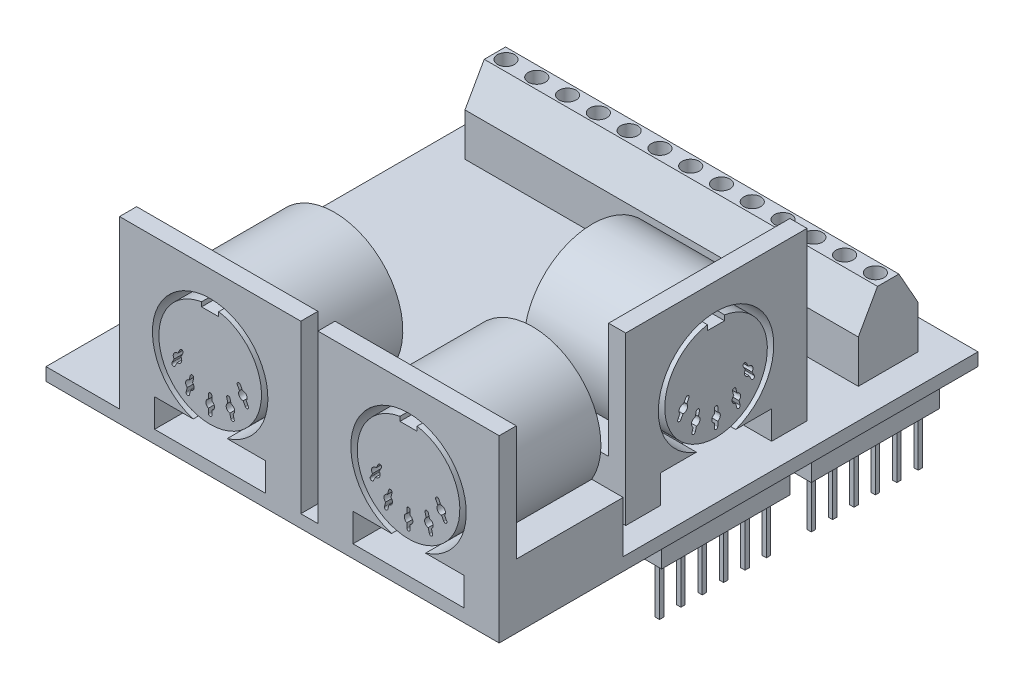
SolidWorks part; units mm, degrees
ref_plane "Front Plane" through (0, 0, 0) normal (0, 0, 1) x (1, 0, 0)
ref_plane "Top Plane" through (0, 0, 0) normal (0, 1, 0) x (1, 0, 0)
ref_plane "Right Plane" through (0, 0, 0) normal (1, 0, 0) x (0, 0, -1)
sketch "Sketch1" plane through (0, 0, 0) normal (0, 1, 0) x (1, 0, 0)
  line L1 (-26.5, -28) -> (26.5, -28)
  line L2 (-26.5, -28) -> (-26.5, 28)
  line L3 (-26.5, 28) -> (26.5, 28)
  line L4 (26.5, -28) -> (26.5, 28)
  line L5 (-26.5, -28) -> (26.5, 28) construction
  line L6 (-26.5, 28) -> (26.5, -28) construction
  point P0 (0, 0)
  dimension "D1" = 53
  dimension "D2" = 56
extrude "Boss-Extrude1" add sketch "Sketch1" along normal blind 1.5
sketch "Sketch2" plane through (0, 1.5, 0) normal (0, 1, 0) x (1, 0, 0)
  line L0 (-26.5, 28) -> (-26.5, -28) construction
  line L1 (-23, 24.5) -> (23, 24.5)
  line L2 (-23, 24.5) -> (-23, 17.5)
  line L3 (-23, 17.5) -> (23, 17.5)
  line L4 (23, 24.5) -> (23, 17.5)
  line L5 (26.5, -28) -> (26.5, 28) construction
  line L6 (26.5, 28) -> (-26.5, 28) construction
  dimension "D1" = 3.5
  dimension "D2" = 3.5
  dimension "D3" = 3.5
  dimension "D4" = 7
extrude "Boss-Extrude2" add sketch "Sketch2" along normal blind 5
sketch "Sketch4" plane through (-23, 0, 0) normal (-1, 0, 0) x (0, 0, 1)
  line L0 (-24.5, 6.5) -> (-17.5, 6.5)
  line L1 (-17.5, 6.5) -> (-19.75, 10.5)
  line L2 (-19.75, 10.5) -> (-22.25, 10.5)
  line L3 (-22.25, 10.5) -> (-24.5, 6.5)
  line L4 (-21, 10.5) -> (-21, 6.5) construction
  dimension "D1" = 4
  dimension "D2" = 2.5
extrude "Boss-Extrude3" add sketch "Sketch4" against normal up to surface (46 mm away) up to face at (23, 4, -21)
sketch "Sketch5" plane through (0, 10.5, 0) normal (0, 1, 0) x (1, 0, 0)
  line L0 (-23, 21) -> (23, 21) construction
  line L1 (-23, 24.5) -> (-23, 17.5) construction
  line L2 (23, 22.25) -> (23, 19.75) construction
  circle A0 centre (-21.7, 21) radius 1
  circle A1 centre (-18.1, 21) radius 1
  circle A2 centre (-14.5, 21) radius 1
  circle A3 centre (-10.9, 21) radius 1
  circle A4 centre (-7.3, 21) radius 1
  circle A5 centre (-3.7, 21) radius 1
  circle A6 centre (-0.1, 21) radius 1
  circle A7 centre (3.5, 21) radius 1
  circle A8 centre (7.1, 21) radius 1
  circle A9 centre (10.7, 21) radius 1
  circle A10 centre (14.3, 21) radius 1
  circle A11 centre (17.9, 21) radius 1
  circle A12 centre (21.5, 21) radius 1
  dimension "D1" = 2
  dimension "D2" = 1.3
  dimension "D3" = 13
extrude "Cut-Extrude1" cut sketch "Sketch5" against normal blind 2
sketch "Sketch6" plane through (0, 0, 28) normal (0, 0, 1) x (1, 0, 0)
  line L0 (-26.5, 1.5) -> (26.5, 1.5) construction
  line L1 (-17.9, 1.5) -> (3.3, 1.5)
  line L2 (-17.9, 1.5) -> (-17.9, 21)
  line L3 (-17.9, 21) -> (3.3, 21)
  line L4 (3.3, 1.5) -> (3.3, 21)
  line L5 (-23, 1.5) -> (23, 1.5) construction
  line L6 (5.3, 1.5) -> (26.5, 1.5)
  line L7 (5.3, 1.5) -> (5.3, 21)
  line L8 (5.3, 21) -> (26.5, 21)
  line L9 (26.5, 1.5) -> (26.5, 21)
  dimension "D1" = 21.2
  dimension "D2" = 19.5
  dimension "D3" = 21.2
  dimension "D4" = 19.5
  dimension "D5" = 2
extrude "Boss-Extrude4" add sketch "Sketch6" against normal blind 2 separate body
sketch "Sketch7" plane through (0, 0, 26) normal (0, 0, -1) x (-1, 0, 0)
  line L0 (-15.9, 21) -> (-15.9, 1.5) construction
  line L1 (-26.5, 21) -> (-5.3, 21) construction
  line L2 (-23, 1.5) -> (23, 1.5) construction
  line L3 (-15.9, 11.5) -> (7.2714, 11.5) construction
  line L4 (7.3, 21) -> (7.3, 7.5) construction
  line L5 (-3.3, 21) -> (17.9, 21) construction
  line L7 (-5.3, 21) -> (-5.3, 1.5) construction
  line L8 (-26.5, 1.5) -> (-5.3, 1.5)
  line L9 (-26.5, 1.5) -> (-26.5, 7.5)
  line L10 (-26.5, 7.5) -> (-22.8282, 7.5)
  line L12 (-5.3, 1.5) -> (-5.3, 7.5)
  line L13 (-8.9718, 7.5) -> (-5.3, 7.5)
  line L14 (-26.5, 1.5) -> (26.5, 1.5) construction
  line L15 (17.9, 7.5) -> (14.1996, 7.5)
  line L16 (17.9, 7.5) -> (17.9, 1.5)
  line L17 (17.9, 1.5) -> (-3.3, 1.5)
  line L18 (-3.3, 7.5) -> (-3.3, 1.5)
  line L19 (-3.3, 1.5) -> (-3.3, 21) construction
  line L20 (17.9, 21) -> (17.9, 1.5) construction
  line L21 (0.3432, 7.5) -> (-3.3, 7.5)
  line L22 (7.3, 3.5001) -> (7.3, 1.5) construction
  arc A0 (-8.9718, 7.5) -> (-22.8282, 7.5) centre (-15.9, 11.5) ccw
  arc A1 (14.1996, 7.5) -> (0.3432, 7.5) centre (7.2714, 11.5) ccw
  point P6 (-15.9, 11.5)
  dimension "D2" = 16
  dimension "D3" = 16
  dimension "D1" = 10
  dimension "D4" = 6
extrude "Boss-Extrude5" add sketch "Sketch7" along normal blind 12.5
sketch "Sketch8" plane through (0, 0, 28) normal (0, 0, 1) x (1, 0, 0)
  line L0 (-17.9, 21) -> (3.3, 1.5) construction
  line L1 (3.3, 21) -> (-17.9, 1.5) construction
  line L2 (-7.3, 17.25) -> (-7.3, 16.65) construction
  line L3 (-8.3, 16.65) -> (-6.3, 16.65)
  line L4 (-6.3, 16.65) -> (-6.3, 17.1661)
  line L5 (-8.3, 16.65) -> (-8.3, 17.1661)
  line L6 (-11.1219, 10.0698) -> (-3.4781, 10.0698) construction
  line L7 (-9.6748, 8.0313) -> (-4.9252, 8.0313) construction
  line L8 (-11.1219, 10.0698) -> (-9.6748, 8.0313) construction
  line L9 (-9.6748, 8.0313) -> (-7.3, 7.25) construction
  line L10 (-7.3, 7.25) -> (-4.9252, 8.0313) construction
  line L11 (-4.9252, 8.0313) -> (-3.4781, 10.0698) construction
  line L12 (-7.3, 6.25) -> (-7.3, 8.25) construction
  line L13 (-7.5, 6.25) -> (-7.5, 6.7917)
  line L14 (-7.1, 6.25) -> (-7.1, 6.7917)
  line L15 (-4.6757, 7.0629) -> (-5.1747, 8.9996) construction
  line L16 (-4.8694, 7.013) -> (-5.0046, 7.5376)
  line L17 (-4.4821, 7.1128) -> (-4.6172, 7.6374)
  line L18 (-3.0082, 9.1871) -> (-3.9479, 10.9526) construction
  line L19 (-3.1847, 9.0931) -> (-3.4393, 9.5713)
  line L20 (-2.8316, 9.2811) -> (-3.0862, 9.7593)
  line L21 (-9.9243, 7.0629) -> (-9.4253, 8.9996) construction
  line L22 (-10.1179, 7.1128) -> (-9.9828, 7.6374)
  line L23 (-9.7306, 7.013) -> (-9.5954, 7.5376)
  line L24 (-11.5918, 9.1871) -> (-10.6521, 10.9526) construction
  line L25 (-11.7684, 9.2811) -> (-11.5138, 9.7593)
  line L26 (-11.4153, 9.0931) -> (-11.1607, 9.5713)
  line L27 (-7.3, 17.25) -> (-10.6521, 10.9526) construction
  line L28 (-7.3, 17.25) -> (-3.9479, 10.9526) construction
  line L29 (-7.3, 17.25) -> (-9.4253, 8.9996) construction
  line L30 (-7.3, 17.25) -> (-5.1747, 8.9996) construction
  line L31 (-11.0832, 10.5683) -> (-10.8286, 11.0465)
  line L32 (-10.7301, 10.3804) -> (-10.4755, 10.8586)
  line L33 (4.3, 1.5) -> (4.3, 27.7192) construction
  line L34 (-9.7542, 8.5249) -> (-9.619, 9.0495)
  line L35 (-9.3668, 8.4251) -> (-9.2317, 8.9497)
  line L36 (3.3, 1.5) -> (5.3, 1.5) construction
  line L37 (15.9, 1.5) -> (15.9, 11.25) construction
  line L38 (-7.5, 7.7083) -> (-7.5, 8.25)
  line L39 (-7.1, 7.7083) -> (-7.1, 8.25)
  line L40 (15.9, 17.25) -> (13.7747, 8.9996) construction
  line L41 (15.9, 17.25) -> (18.0253, 8.9996) construction
  line L42 (-5.2332, 8.4251) -> (-5.3683, 8.9497)
  line L43 (-4.8458, 8.5249) -> (-4.981, 9.0495)
  line L44 (15.9, 17.25) -> (12.5479, 10.9526) construction
  line L45 (15.9, 17.25) -> (19.2521, 10.9526) construction
  line L46 (-3.8699, 10.3804) -> (-4.1245, 10.8586)
  line L47 (-3.5168, 10.5683) -> (-3.7714, 11.0465)
  line L48 (20.1918, 9.1871) -> (19.2521, 10.9526) construction
  line L49 (18.5243, 7.0629) -> (18.0253, 8.9996) construction
  line L50 (11.6082, 9.1871) -> (12.5479, 10.9526) construction
  line L51 (13.2757, 7.0629) -> (13.7747, 8.9996) construction
  line L52 (15.9, 6.25) -> (15.9, 8.25) construction
  line L53 (13.5252, 8.0313) -> (12.0781, 10.0698) construction
  line L54 (15.9, 7.25) -> (13.5252, 8.0313) construction
  line L55 (18.2748, 8.0313) -> (15.9, 7.25) construction
  line L56 (19.7219, 10.0698) -> (18.2748, 8.0313) construction
  line L57 (18.2748, 8.0313) -> (13.5252, 8.0313) construction
  line L58 (19.7219, 10.0698) -> (12.0781, 10.0698) construction
  line L59 (15.9, 17.25) -> (15.9, 16.65) construction
  line L60 (17.89, 4.8) -> (22.4, 4.8)
  line L61 (22.4, 4.8) -> (22.4, 1.5)
  line L62 (9.4, 4.8) -> (13.91, 4.8)
  line L63 (9.4, 1.5) -> (9.4, 4.8)
  line L64 (22.4, 1.5) -> (9.4, 1.5)
  line L65 (12.1168, 10.5683) -> (12.3714, 11.0465)
  line L66 (12.4699, 10.3804) -> (12.7245, 10.8586)
  line L67 (13.4458, 8.5249) -> (13.581, 9.0495)
  line L68 (13.8332, 8.4251) -> (13.9683, 8.9497)
  line L69 (15.7, 7.7083) -> (15.7, 8.25)
  line L70 (16.1, 7.7083) -> (16.1, 8.25)
  line L71 (17.9668, 8.4251) -> (17.8317, 8.9497)
  line L72 (18.3542, 8.5249) -> (18.219, 9.0495)
  line L73 (19.3301, 10.3804) -> (19.0755, 10.8586)
  line L74 (19.6832, 10.5683) -> (19.4286, 11.0465)
  line L75 (20.0153, 9.0931) -> (19.7607, 9.5713)
  line L76 (20.3684, 9.2811) -> (20.1138, 9.7593)
  line L77 (18.3306, 7.013) -> (18.1954, 7.5376)
  line L78 (18.7179, 7.1128) -> (18.5828, 7.6374)
  line L79 (11.4316, 9.2811) -> (11.6862, 9.7593)
  line L80 (11.7847, 9.0931) -> (12.0393, 9.5713)
  line L81 (13.0821, 7.1128) -> (13.2172, 7.6374)
  line L82 (-17.9, 1.5) -> (3.3, 1.5) construction
  line L83 (-13.8, 1.5) -> (-0.8, 1.5)
  line L84 (-0.8, 1.5) -> (-0.8, 4.8)
  line L85 (-0.8, 4.8) -> (-5.31, 4.8)
  line L86 (-13.8, 4.8) -> (-13.8, 1.5)
  line L87 (-7.3, 1.5) -> (-7.3, 11.25) construction
  line L88 (-9.29, 4.8) -> (-13.8, 4.8)
  line L89 (13.4694, 7.013) -> (13.6046, 7.5376)
  line L90 (15.7, 6.25) -> (15.7, 6.7917)
  line L91 (16.1, 6.25) -> (16.1, 6.7917)
  line L92 (16.9, 16.65) -> (16.9, 17.1661)
  line L93 (14.9, 16.65) -> (14.9, 17.1661)
  line L94 (16.9, 16.65) -> (14.9, 16.65)
  arc A0 (-5.31, 4.8) -> (-9.29, 4.8) centre (-7.3, 11.25) ccw
  arc A1 (-8.3, 17.1661) -> (-6.3, 17.1661) centre (-7.3, 11.25) ccw
  arc A2 (-7.5, 7.7083) -> (-7.5, 6.7917) centre (-7.3, 7.25) ccw
  arc A3 (-9.5954, 7.5376) -> (-9.3668, 8.4251) centre (-9.6748, 8.0313) ccw
  arc A4 (-4.8005, 7.5471) -> (-4.8458, 8.5249) centre (-4.9252, 8.0313) ccw
  arc A5 (-3.0862, 9.7593) -> (-3.5168, 10.5683) centre (-3.4781, 10.0698) ccw
  arc A6 (-11.0832, 10.5683) -> (-11.5138, 9.7593) centre (-11.1219, 10.0698) ccw
  circle A7 centre (-7.3, 11.25) radius 4 construction
  arc A8 (-7.5, 6.25) -> (-7.1, 6.25) centre (-7.3, 6.25) ccw
  arc A9 (-7.1, 8.25) -> (-7.5, 8.25) centre (-7.3, 8.25) ccw
  arc A10 (-4.8694, 7.013) -> (-4.4821, 7.1128) centre (-4.6757, 7.0629) ccw
  arc A11 (-4.981, 9.0495) -> (-5.3683, 8.9497) centre (-5.1747, 8.9996) ccw
  arc A12 (-3.1847, 9.0931) -> (-2.8316, 9.2811) centre (-3.0082, 9.1871) ccw
  arc A13 (-3.7714, 11.0465) -> (-4.1245, 10.8586) centre (-3.9479, 10.9526) ccw
  arc A14 (-10.1179, 7.1128) -> (-9.7306, 7.013) centre (-9.9243, 7.0629) ccw
  arc A15 (-9.2317, 8.9497) -> (-9.619, 9.0495) centre (-9.4253, 8.9996) ccw
  arc A16 (-11.7684, 9.2811) -> (-11.4153, 9.0931) centre (-11.5918, 9.1871) ccw
  arc A17 (-10.4755, 10.8586) -> (-10.8286, 11.0465) centre (-10.6521, 10.9526) ccw
  arc A18 (-11.1607, 9.5713) -> (-10.7301, 10.3804) centre (-11.1219, 10.0698) ccw
  arc A19 (-9.7542, 8.5249) -> (-9.9828, 7.6374) centre (-9.6748, 8.0313) ccw
  arc A20 (-7.1, 6.7917) -> (-7.1, 7.7083) centre (-7.3, 7.25) ccw
  arc A21 (-5.2332, 8.4251) -> (-5.0046, 7.5376) centre (-4.9252, 8.0313) ccw
  arc A22 (-3.8699, 10.3804) -> (-3.4393, 9.5713) centre (-3.4781, 10.0698) ccw
  circle A23 centre (15.9, 11.25) radius 4 construction
  arc A24 (12.4699, 10.3804) -> (12.0393, 9.5713) centre (12.0781, 10.0698) cw
  arc A25 (13.8332, 8.4251) -> (13.6046, 7.5376) centre (13.5252, 8.0313) cw
  arc A26 (15.7, 6.7917) -> (15.7, 7.7083) centre (15.9, 7.25) cw
  arc A27 (18.3542, 8.5249) -> (18.5828, 7.6374) centre (18.2748, 8.0313) cw
  arc A28 (19.7607, 9.5713) -> (19.3301, 10.3804) centre (19.7219, 10.0698) cw
  arc A29 (19.0755, 10.8586) -> (19.4286, 11.0465) centre (19.2521, 10.9526) cw
  arc A30 (20.3684, 9.2811) -> (20.0153, 9.0931) centre (20.1918, 9.1871) cw
  arc A31 (17.8317, 8.9497) -> (18.219, 9.0495) centre (18.0253, 8.9996) cw
  arc A32 (18.7179, 7.1128) -> (18.3306, 7.013) centre (18.5243, 7.0629) cw
  arc A33 (12.3714, 11.0465) -> (12.7245, 10.8586) centre (12.5479, 10.9526) cw
  arc A34 (11.7847, 9.0931) -> (11.4316, 9.2811) centre (11.6082, 9.1871) cw
  arc A35 (13.581, 9.0495) -> (13.9683, 8.9497) centre (13.7747, 8.9996) cw
  arc A36 (13.4694, 7.013) -> (13.0821, 7.1128) centre (13.2757, 7.0629) cw
  arc A37 (15.7, 8.25) -> (16.1, 8.25) centre (15.9, 8.25) cw
  arc A38 (16.1, 6.25) -> (15.7, 6.25) centre (15.9, 6.25) cw
  arc A39 (19.6832, 10.5683) -> (20.1138, 9.7593) centre (19.7219, 10.0698) cw
  arc A40 (11.6862, 9.7593) -> (12.1168, 10.5683) centre (12.0781, 10.0698) cw
  arc A41 (13.4005, 7.5471) -> (13.4458, 8.5249) centre (13.5252, 8.0313) cw
  arc A42 (18.1954, 7.5376) -> (17.9668, 8.4251) centre (18.2748, 8.0313) cw
  arc A43 (16.1, 7.7083) -> (16.1, 6.7917) centre (15.9, 7.25) cw
  arc A44 (16.9, 17.1661) -> (14.9, 17.1661) centre (15.9, 11.25) cw
  arc A45 (13.91, 4.8) -> (17.89, 4.8) centre (15.9, 11.25) cw
  point P8 (-7.3, 11.25)
  point P30 (-7.3, 7.25)
  point P37 (-4.9252, 8.0313)
  point P44 (-3.4781, 10.0698)
  point P50 (-9.6748, 8.0313)
  point P58 (-11.1219, 10.0698)
  dimension "D1" = 13.5
  dimension "D2" = 12
  dimension "D4" = 1
  dimension "D5" = 8
  dimension "D8" = 0.2
  dimension "D3" = 2
  dimension "D6" = 2.5
  dimension "D7" = 2
  dimension "D9" = 3.3
  dimension "D10" = 13
  dimension "D11" = 0.6
extrude "Cut-Extrude2" cut sketch "Sketch8" against normal blind 5
sketch "Sketch9" plane through (26.5, 0, 0) normal (1, 0, 0) x (0, 0, -1)
  line L0 (-13.5, 1.5) -> (28, 1.5) construction
  line L1 (-10.2, 1.5) -> (11, 1.5)
  line L2 (-10.2, 1.5) -> (-10.2, 21)
  line L3 (-10.2, 21) -> (11, 21)
  line L4 (11, 1.5) -> (11, 21)
  line L5 (-26, 21) -> (-28, 21) construction
  line L7 (-28, 21) -> (-28, 0) construction
  dimension "D1" = 21.2
  dimension "D2" = 39
extrude "Boss-Extrude6" add sketch "Sketch9" against normal blind 2 from offset 3 separate body offset against normal yes
sketch "Sketch11" plane through (21.5, 0, 0) normal (-1, 0, 0) x (0, 0, 1)
  line L0 (-0.4, 21) -> (-0.4, 1.5) construction
  line L1 (-11, 21) -> (10.2, 21) construction
  line L2 (10.2, 1.5) -> (-11, 1.5) construction
  line L3 (10.2, 21) -> (10.2, 1.5) construction
  line L4 (-11, 1.5) -> (10.2, 1.5)
  line L5 (-11, 1.5) -> (-11, 7.5)
  line L6 (-11, 7.5) -> (-7.3282, 7.5)
  line L7 (10.2, 1.5) -> (10.2, 7.5)
  line L8 (6.5282, 7.5) -> (10.2, 7.5)
  arc A0 (6.5282, 7.5) -> (-7.3282, 7.5) centre (-0.4, 11.5) ccw
  dimension "D2" = 16
  dimension "D1" = 10
  dimension "D3" = 6
extrude "Boss-Extrude7" add sketch "Sketch11" along normal blind 12.5
sketch "Sketch13" plane through (23.5, 0, 0) normal (1, 0, 0) x (0, 0, -1)
  line L0 (-10.2, 21) -> (11, 1.5) construction
  line L1 (-10.2, 1.5) -> (11, 1.5) construction
  line L2 (0.3632, 16.1486) -> (0.3632, 1.5) construction
  line L3 (-6.1, 1.5) -> (6.8265, 1.5)
  line L7 (0.3632, 17.0631) -> (0.3632, 16.4631) construction
  line L8 (-0.6368, 16.4631) -> (1.3632, 16.4631)
  line L9 (1.3632, 16.4631) -> (1.3632, 17.0631)
  line L10 (-0.6368, 16.4631) -> (-0.6368, 17.0631)
  line L11 (-3.4587, 9.9668) -> (4.1852, 9.9668) construction
  line L12 (-2.0116, 7.9283) -> (2.738, 7.9283) construction
  line L13 (-3.4587, 9.9668) -> (-2.0116, 7.9283) construction
  line L14 (-2.0116, 7.9283) -> (0.3632, 7.147) construction
  line L15 (0.3632, 7.147) -> (2.738, 7.9283) construction
  line L16 (2.738, 7.9283) -> (4.1852, 9.9668) construction
  line L17 (0.3632, 6.147) -> (0.3632, 8.147) construction
  line L18 (0.1633, 6.1525) -> (0.1633, 6.6887)
  line L19 (0.5631, 6.1534) -> (0.5631, 6.6887)
  line L20 (2.9896, 6.9604) -> (2.4864, 8.8961) construction
  line L21 (2.7897, 6.9582) -> (2.6661, 7.4335)
  line L22 (3.186, 6.9982) -> (3.0465, 7.5348)
  line L23 (4.6594, 9.0864) -> (3.711, 10.8473) construction
  line L24 (4.4753, 9.0081) -> (4.2273, 9.4686)
  line L25 (4.8354, 9.1812) -> (4.5786, 9.6582)
  line L26 (-2.2632, 6.9604) -> (-1.7599, 8.8961) construction
  line L27 (-2.4567, 7.0108) -> (-2.3204, 7.535)
  line L28 (-2.0696, 6.9101) -> (-1.9333, 7.4344)
  line L29 (-3.9329, 9.0864) -> (-2.9845, 10.8473) construction
  line L30 (-4.1058, 9.1869) -> (-3.852, 9.6581)
  line L31 (-3.7568, 8.9916) -> (-3.4999, 9.4685)
  line L32 (0.3632, 17.0631) -> (-2.9845, 10.8473) construction
  line L33 (0.3632, 17.0631) -> (3.711, 10.8473) construction
  line L34 (0.3632, 17.0631) -> (-1.7599, 8.8961) construction
  line L35 (0.3632, 17.0631) -> (2.4864, 8.8961) construction
  line L36 (-3.4174, 10.4651) -> (-3.1636, 10.9363)
  line L37 (-3.0653, 10.2755) -> (-2.8084, 10.7524)
  line L38 (-2.0897, 8.4221) -> (-1.9519, 8.9523)
  line L39 (-1.7027, 8.3215) -> (-1.5664, 8.8458)
  line L40 (0.1633, 7.6053) -> (0.1633, 8.153)
  line L41 (0.5631, 7.6053) -> (0.5631, 8.1534)
  line L42 (2.4366, 8.3272) -> (2.2866, 8.9043)
  line L43 (2.8159, 8.4222) -> (2.6828, 8.9339)
  line L44 (3.7918, 10.2755) -> (3.5349, 10.7524)
  line L45 (4.144, 10.4651) -> (3.8871, 10.9421)
  line L46 (-6.1368, 1.5) -> (6.8632, 1.5)
  line L47 (6.8632, 1.5) -> (6.8632, 4.8)
  line L48 (6.8632, 4.8) -> (2.6606, 4.8)
  line L49 (-6.1368, 4.8) -> (-6.1368, 1.5)
  line L50 (0.3632, 1.5) -> (0.3632, 11.147) construction
  line L51 (-1.9342, 4.8) -> (-6.1368, 4.8)
  arc A2 (2.6606, 4.8) -> (-1.9342, 4.8) centre (0.3632, 11.147) ccw
  arc A3 (-0.6368, 17.0631) -> (1.3632, 17.0631) centre (0.3632, 11.147) ccw
  arc A4 (0.1633, 7.6053) -> (0.1633, 6.6887) centre (0.3632, 7.147) ccw
  arc A5 (-1.9333, 7.4344) -> (-1.7027, 8.3215) centre (-2.0116, 7.9283) ccw
  arc A6 (3.0465, 7.5348) -> (2.8159, 8.4222) centre (2.738, 7.9283) ccw
  arc A7 (4.5786, 9.6582) -> (4.144, 10.4651) centre (4.1852, 9.9668) ccw
  arc A8 (-3.4174, 10.4651) -> (-3.852, 9.6581) centre (-3.4587, 9.9668) ccw
  circle A9 centre (0.3632, 11.147) radius 4 construction
  arc A10 (0.1633, 6.1525) -> (0.5631, 6.1534) centre (0.3632, 6.147) ccw
  arc A11 (0.5631, 8.1534) -> (0.1633, 8.153) centre (0.3632, 8.147) ccw
  arc A12 (2.7897, 6.9582) -> (3.186, 6.9982) centre (2.9896, 6.9604) ccw
  arc A13 (2.6828, 8.9339) -> (2.2866, 8.9043) centre (2.4864, 8.8961) ccw
  arc A14 (4.4753, 9.0081) -> (4.8354, 9.1812) centre (4.6594, 9.0864) ccw
  arc A15 (3.8871, 10.9421) -> (3.5349, 10.7524) centre (3.711, 10.8473) ccw
  arc A16 (-2.4567, 7.0108) -> (-2.0696, 6.9101) centre (-2.2632, 6.9604) ccw
  arc A17 (-1.5664, 8.8458) -> (-1.9519, 8.9523) centre (-1.7599, 8.8961) ccw
  arc A18 (-4.1058, 9.1869) -> (-3.7568, 8.9916) centre (-3.9329, 9.0864) ccw
  arc A19 (-2.8084, 10.7524) -> (-3.1636, 10.9363) centre (-2.9845, 10.8473) ccw
  arc A20 (-3.4999, 9.4685) -> (-3.0653, 10.2755) centre (-3.4587, 9.9668) ccw
  arc A21 (-2.0897, 8.4221) -> (-2.3204, 7.535) centre (-2.0116, 7.9283) ccw
  arc A22 (0.5631, 6.6887) -> (0.5631, 7.6053) centre (0.3632, 7.147) ccw
  arc A23 (2.4366, 8.3272) -> (2.6661, 7.4335) centre (2.738, 7.9283) ccw
  arc A24 (3.7918, 10.2755) -> (4.2273, 9.4686) centre (4.1852, 9.9668) ccw
  point P15 (0.3632, 11.147)
  point P35 (0.3632, 7.147)
  point P42 (2.738, 7.9283)
  point P49 (4.1852, 9.9668)
  point P55 (-2.0116, 7.9283)
  point P63 (-3.4587, 9.9668)
  point P93 (0.4, 11.25)
  line M4 (-10.2, 1.5) -> (11, 1.5)
  dimension "D2" = 13
  dimension "D6" = 1
  dimension "D7" = 8
  dimension "D10" = 0.2
  dimension "D3" = 6.75
  dimension "D12" = 6
  dimension "D13" = 0.2
  dimension "D4" = 3.3
  dimension "D5" = 2
  dimension "D8" = 2.5
  dimension "D9" = 2
  dimension "D11" = 0.6
extrude "Cut-Extrude3" cut sketch "Sketch13" against normal blind 5 contours L48 A2 L51 L49 L47 A3 L10 L8 L9 M4 | L38 A21 L27 A16 L28 A5 L39 A17 | L31 A20 L37 A19 L36 A8 L30 A18 | L19 A22 L41 A11 L40 A4 L18 A10 | L42 A23 L21 A12 L22 A6 L43 A13 | L44 A24 L24 A14 L25 A7 L45 A15
sketch "Sketch14" plane through (0, 0, 0) normal (0, -1, 0) x (1, 0, 0)
  line L0 (25.5, 28) -> (25.5, -28) construction
  line L3 (-26.5, 28) -> (26.5, 28) construction
  line L4 (26.5, -28) -> (-26.5, -28) construction
  line L5 (-25.5, 28) -> (-25.5, -28) construction
  line L6 (26.5, 28) -> (26.5, -28) construction
  line L7 (-26.5, -28) -> (-26.5, 28) construction
  line L9 (-25.5, 18) -> (-23, 18)
  line L10 (-25.5, 18) -> (-25.5, -2)
  line L11 (-25.5, -2) -> (-23, -2)
  line L12 (-23, 18) -> (-23, -2)
  line L13 (25.5, 8) -> (23, 8)
  line L14 (25.5, 8) -> (25.5, -7)
  line L15 (25.5, -7) -> (23, -7)
  line L16 (23, 8) -> (23, -7)
  line L17 (25.5, -9.5) -> (23, -9.5)
  line L18 (25.5, -9.5) -> (25.5, -24.5)
  line L19 (25.5, -24.5) -> (23, -24.5)
  line L20 (23, -9.5) -> (23, -24.5)
  line L21 (-25.5, -4.5) -> (-23, -4.5)
  line L22 (-25.5, -4.5) -> (-25.5, -24.5)
  line L23 (-25.5, -24.5) -> (-23, -24.5)
  line L24 (-23, -4.5) -> (-23, -24.5)
  dimension "D1" = 1
  dimension "D2" = 1
  dimension "D3" = 2.5
  dimension "D4" = 20
  dimension "D5" = 15
  dimension "D6" = 3.5
  dimension "D7" = 15
  dimension "D8" = 2.5
  dimension "D9" = 10
  dimension "D10" = 2.5
  dimension "D11" = 20
  dimension "D12" = 2.5
  dimension "D13" = 20
  dimension "D14" = 3.5
extrude "Boss-Extrude8" add sketch "Sketch14" along normal blind 3
sketch "Sketch15" plane through (0, -3, 0) normal (0, -1, 0) x (1, 0, 0)
  line L0 (24.25, 8) -> (24.25, -24.5) construction
  line L1 (25.5, 8) -> (23, 8) construction
  line L2 (23, -24.5) -> (25.5, -24.5) construction
  line L3 (24, 4.75) -> (24.5, 4.75)
  line L4 (24, 7.25) -> (24.5, 7.25)
  line L5 (24, 7.25) -> (24, 6.75)
  line L6 (24, 6.75) -> (24.5, 6.75)
  line L7 (24.5, 7.25) -> (24.5, 6.75)
  line L8 (24, 7.25) -> (24.5, 6.75) construction
  line L9 (24, 6.75) -> (24.5, 7.25) construction
  line L10 (24, 4.75) -> (24, 4.25)
  line L11 (24, 4.25) -> (24.5, 4.25)
  line L12 (24.5, 4.75) -> (24.5, 4.25)
  line L13 (24, 4.75) -> (24.5, 4.25) construction
  line L14 (24, 4.25) -> (24.5, 4.75) construction
  line L15 (24, 2.25) -> (24.5, 2.25)
  line L16 (24, 2.25) -> (24, 1.75)
  line L17 (24, 1.75) -> (24.5, 1.75)
  line L18 (24.5, 2.25) -> (24.5, 1.75)
  line L19 (24, 2.25) -> (24.5, 1.75) construction
  line L20 (24, 1.75) -> (24.5, 2.25) construction
  line L21 (24, -0.25) -> (24.5, -0.25)
  line L22 (24, -0.25) -> (24, -0.75)
  line L23 (24, -0.75) -> (24.5, -0.75)
  line L24 (24.5, -0.25) -> (24.5, -0.75)
  line L25 (24, -0.25) -> (24.5, -0.75) construction
  line L26 (24, -0.75) -> (24.5, -0.25) construction
  line L27 (24, -2.75) -> (24.5, -2.75)
  line L28 (24, -2.75) -> (24, -3.25)
  line L29 (24, -3.25) -> (24.5, -3.25)
  line L30 (24.5, -2.75) -> (24.5, -3.25)
  line L31 (24, -2.75) -> (24.5, -3.25) construction
  line L32 (24, -3.25) -> (24.5, -2.75) construction
  line L33 (24, -5.25) -> (24.5, -5.25)
  line L34 (24, -5.25) -> (24, -5.75)
  line L35 (24, -5.75) -> (24.5, -5.75)
  line L36 (24.5, -5.25) -> (24.5, -5.75)
  line L37 (24, -5.25) -> (24.5, -5.75) construction
  line L38 (24, -5.75) -> (24.5, -5.25) construction
  line L42 (25.5, -9.5) -> (23, -9.5) construction
  line L43 (24, -10.5) -> (24.5, -10.5)
  line L44 (24, -10.5) -> (24, -11)
  line L45 (24, -11) -> (24.5, -11)
  line L46 (24.5, -10.5) -> (24.5, -11)
  line L47 (24, -10.5) -> (24.5, -11) construction
  line L48 (24, -11) -> (24.5, -10.5) construction
  line L49 (24, -13) -> (24, -13.5)
  line L50 (24, -13.5) -> (24.5, -13.5)
  line L51 (24.5, -13) -> (24.5, -13.5)
  line L52 (24, -13) -> (24.5, -13)
  line L53 (24, -15.5) -> (24, -16)
  line L54 (24, -16) -> (24.5, -16)
  line L55 (24.5, -15.5) -> (24.5, -16)
  line L56 (24, -15.5) -> (24.5, -15.5)
  line L57 (24, -18) -> (24, -18.5)
  line L58 (24, -18.5) -> (24.5, -18.5)
  line L59 (24.5, -18) -> (24.5, -18.5)
  line L60 (24, -18) -> (24.5, -18)
  line L61 (24, -20.5) -> (24, -21)
  line L62 (24, -21) -> (24.5, -21)
  line L63 (24.5, -20.5) -> (24.5, -21)
  line L64 (24, -20.5) -> (24.5, -20.5)
  line L65 (24, -23) -> (24, -23.5)
  line L66 (24, -23.5) -> (24.5, -23.5)
  line L67 (24.5, -23) -> (24.5, -23.5)
  line L68 (24, -23) -> (24.5, -23)
  line L70 (-24.25, 18) -> (-24.25, -24.5) construction
  line L71 (-23, 18) -> (-25.5, 18) construction
  line L72 (-25.5, -24.5) -> (-23, -24.5) construction
  line L73 (-24.5, 14.5) -> (-24, 14.5)
  line L74 (-24.5, 17) -> (-24, 17)
  line L75 (-24.5, 17) -> (-24.5, 16.5)
  line L76 (-24.5, 16.5) -> (-24, 16.5)
  line L77 (-24, 17) -> (-24, 16.5)
  line L78 (-24.5, 17) -> (-24, 16.5) construction
  line L79 (-24.5, 16.5) -> (-24, 17) construction
  line L80 (-24.5, 14.5) -> (-24.5, 14)
  line L81 (-24.5, 14) -> (-24, 14)
  line L82 (-24, 14.5) -> (-24, 14)
  line L83 (-24.5, 14.5) -> (-24, 14) construction
  line L84 (-24.5, 14) -> (-24, 14.5) construction
  line L85 (-24.5, 12) -> (-24, 12)
  line L86 (-24.5, 12) -> (-24.5, 11.5)
  line L87 (-24.5, 11.5) -> (-24, 11.5)
  line L88 (-24, 12) -> (-24, 11.5)
  line L89 (-24.5, 12) -> (-24, 11.5) construction
  line L90 (-24.5, 11.5) -> (-24, 12) construction
  line L91 (-24.5, 9.5) -> (-24, 9.5)
  line L92 (-24.5, 9.5) -> (-24.5, 9)
  line L93 (-24.5, 9) -> (-24, 9)
  line L94 (-24, 9.5) -> (-24, 9)
  line L95 (-24.5, 9.5) -> (-24, 9) construction
  line L96 (-24.5, 9) -> (-24, 9.5) construction
  line L97 (-24.5, 7) -> (-24, 7)
  line L98 (-24.5, 7) -> (-24.5, 6.5)
  line L99 (-24.5, 6.5) -> (-24, 6.5)
  line L100 (-24, 7) -> (-24, 6.5)
  line L101 (-24.5, 7) -> (-24, 6.5) construction
  line L102 (-24.5, 6.5) -> (-24, 7) construction
  line L103 (-24.5, 4.5) -> (-24, 4.5)
  line L104 (-24.5, 4.5) -> (-24.5, 4)
  line L105 (-24.5, 4) -> (-24, 4)
  line L106 (-24, 4.5) -> (-24, 4)
  line L107 (-24.5, 4.5) -> (-24, 4) construction
  line L108 (-24.5, 4) -> (-24, 4.5) construction
  line L109 (-24.5, 2) -> (-24, 2)
  line L110 (-24.5, 2) -> (-24.5, 1.5)
  line L111 (-24.5, 1.5) -> (-24, 1.5)
  line L112 (-24, 2) -> (-24, 1.5)
  line L113 (-24.5, 2) -> (-24, 1.5) construction
  line L114 (-24.5, 1.5) -> (-24, 2) construction
  line L115 (-24.5, -0.5) -> (-24, -0.5)
  line L116 (-24.5, -0.5) -> (-24.5, -1)
  line L117 (-24.5, -1) -> (-24, -1)
  line L118 (-24, -0.5) -> (-24, -1)
  line L119 (-24.5, -0.5) -> (-24, -1) construction
  line L120 (-24.5, -1) -> (-24, -0.5) construction
  line L121 (-24.25, -3.25) -> (-28.1143, -3.25) construction
  line L122 (-24.5, -5.5) -> (-24, -6) construction
  line L123 (-24.5, -6) -> (-24, -5.5) construction
  line L124 (-24.5, -8) -> (-24, -8.5) construction
  line L125 (-24.5, -8.5) -> (-24, -8) construction
  line L126 (-24.5, -10.5) -> (-24, -11) construction
  line L127 (-24.5, -11) -> (-24, -10.5) construction
  line L128 (-24.5, -13) -> (-24, -13.5) construction
  line L129 (-24.5, -13.5) -> (-24, -13) construction
  line L130 (-24.5, -15.5) -> (-24, -16) construction
  line L131 (-24.5, -16) -> (-24, -15.5) construction
  line L132 (-24.5, -18) -> (-24, -18.5) construction
  line L133 (-24.5, -18.5) -> (-24, -18) construction
  line L134 (-24.5, -20.5) -> (-24, -21) construction
  line L135 (-24.5, -21) -> (-24, -20.5) construction
  line L136 (-24.5, -23) -> (-24, -23.5) construction
  line L137 (-24.5, -23.5) -> (-24, -23) construction
  line L138 (-24, -6) -> (-24, -5.5)
  line L139 (-24.5, -5.5) -> (-24, -5.5)
  line L140 (-24.5, -6) -> (-24.5, -5.5)
  line L141 (-24.5, -6) -> (-24, -6)
  line L142 (-24, -8.5) -> (-24, -8)
  line L143 (-24.5, -8) -> (-24, -8)
  line L144 (-24.5, -8.5) -> (-24.5, -8)
  line L145 (-24.5, -8.5) -> (-24, -8.5)
  line L146 (-24, -11) -> (-24, -10.5)
  line L147 (-24.5, -10.5) -> (-24, -10.5)
  line L148 (-24.5, -11) -> (-24.5, -10.5)
  line L149 (-24.5, -11) -> (-24, -11)
  line L150 (-24, -13.5) -> (-24, -13)
  line L151 (-24.5, -13) -> (-24, -13)
  line L152 (-24.5, -13.5) -> (-24.5, -13)
  line L153 (-24.5, -13.5) -> (-24, -13.5)
  line L154 (-24, -16) -> (-24, -15.5)
  line L155 (-24.5, -15.5) -> (-24, -15.5)
  line L156 (-24.5, -16) -> (-24.5, -15.5)
  line L157 (-24.5, -16) -> (-24, -16)
  line L158 (-24, -18.5) -> (-24, -18)
  line L159 (-24.5, -18) -> (-24, -18)
  line L160 (-24.5, -18.5) -> (-24.5, -18)
  line L161 (-24.5, -18.5) -> (-24, -18.5)
  line L162 (-24, -21) -> (-24, -20.5)
  line L163 (-24.5, -20.5) -> (-24, -20.5)
  line L164 (-24.5, -21) -> (-24.5, -20.5)
  line L165 (-24, -23.5) -> (-24, -23)
  line L166 (-24.5, -23) -> (-24, -23)
  line L167 (-24.5, -23.5) -> (-24.5, -23)
  line L168 (-24.5, -23.5) -> (-24, -23.5)
  line L169 (-24.5, -21) -> (-24, -21)
  point P6 (24.25, 7)
  point P13 (24.25, 4.5)
  point P18 (24.25, 2)
  point P23 (24.25, -0.5)
  point P28 (24.25, -3)
  point P33 (24.25, -5.5)
  point P38 (24.25, -10.75)
  point P43 (-24.25, 16.75)
  point P76 (-24.25, 14.25)
  point P81 (-24.25, 11.75)
  point P86 (-24.25, 9.25)
  point P91 (-24.25, 6.75)
  point P96 (-24.25, 4.25)
  point P101 (-24.25, 1.75)
  point P106 (-24.25, -0.75)
  point P143 (-24.25, -5.75)
  point P144 (-24.25, -8.25)
  point P145 (-24.25, -10.75)
  point P146 (-24.25, -13.25)
  point P147 (-24.25, -15.75)
  point P148 (-24.25, -18.25)
  point P149 (-24.25, -20.75)
  point P150 (-24.25, -23.25)
  dimension "D1" = 0.5
  dimension "D2" = 0.5
  dimension "D3" = 1
  dimension "D5" = 0.5
  dimension "D6" = 0.5
  dimension "D7" = 1
  dimension "D9" = 1
  dimension "D10" = 0.5
  dimension "D11" = 0.5
  dimension "D4" = 6
  dimension "D8" = 6
  dimension "D12" = 8
extrude "Boss-Extrude9" add sketch "Sketch15" along normal blind 6
